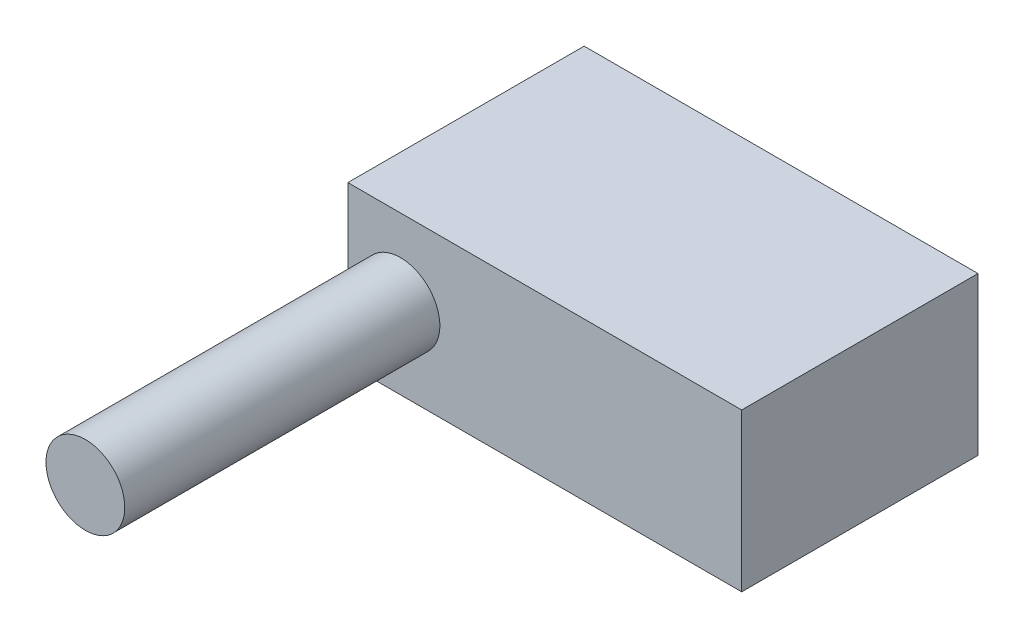
SolidWorks part; units mm, degrees
ref_plane "Front Plane" through (0, 0, 0) normal (0, 0, 1) x (1, 0, 0)
ref_plane "Top Plane" through (0, 0, 0) normal (0, 1, 0) x (1, 0, 0)
ref_plane "Right Plane" through (0, 0, 0) normal (1, 0, 0) x (0, 0, -1)
sketch "Sketch2" plane through (0, 0, 0) normal (0, 1, 0) x (1, 0, 0)
  line L1 (-25, -15) -> (25, -15)
  line L2 (-25, -15) -> (-25, 15)
  line L3 (-25, 15) -> (25, 15)
  line L4 (25, -15) -> (25, 15)
  line L5 (-25, -15) -> (25, 15) construction
  line L6 (-25, 15) -> (25, -15) construction
  point P0 (0, 0)
  dimension "D1" = 50
  dimension "D2" = 30
extrude "Boss-Extrude1" add sketch "Sketch2" along normal blind 20
sketch "Sketch3" plane through (0, 0, 15) normal (0, 0, 1) x (1, 0, 0)
  circle A0 centre (-18.3213, 10.0959) radius 5
  dimension "D1" = 10
extrude "Boss-Extrude2" add sketch "Sketch3" along normal blind 40
